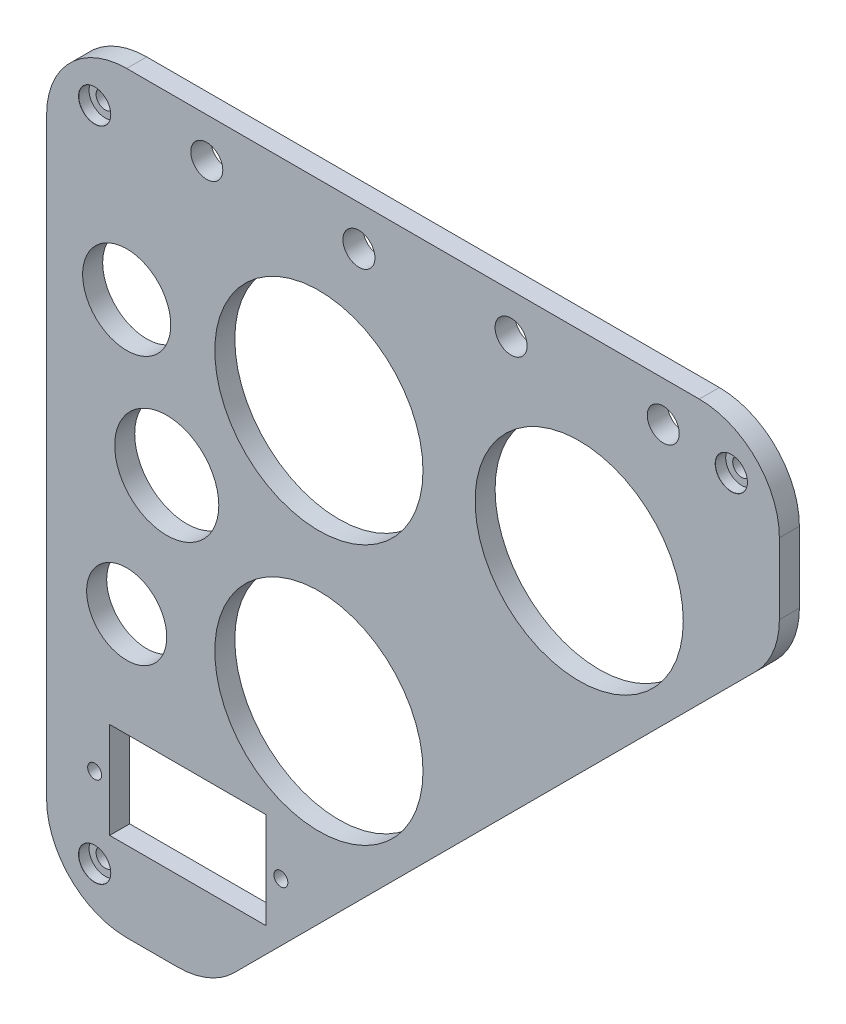
SolidWorks part; units mm, degrees
ref_plane "Piano frontale" through (0, 0, 0) normal (0, 0, 1) x (1, 0, 0)
ref_plane "Piano superiore" through (0, 0, 0) normal (0, 1, 0) x (1, 0, 0)
ref_plane "Piano destro" through (0, 0, 0) normal (1, 0, 0) x (0, 0, -1)
sketch "Schizzo1" plane through (0, 0, 0) normal (0, 0, 1) x (1, 0, 0)
  line L0 (0, 20) -> (0, 168)
  line L1 (20, 188) -> (163, 188)
  line L2 (183, 168) -> (183, 150.2843)
  line L3 (177.1421, 136.1421) -> (46.8579, 5.8579)
  line L4 (32.7157, 0) -> (20, 0)
  arc A0 (0, 168) -> (20, 188) centre (20, 168) cw
  arc A1 (0, 20) -> (20, 0) centre (20, 20) ccw
  arc A2 (46.8579, 5.8579) -> (32.7157, 0) centre (32.7157, 20) cw
  arc A3 (183, 150.2843) -> (177.1421, 136.1421) centre (163, 150.2843) cw
  arc A4 (163, 188) -> (183, 168) centre (163, 168) cw
  point P8 (0, 188)
  point P11 (0, 0)
  point P14 (41, 0)
  point P17 (183, 142)
  point P20 (183, 188)
  dimension "D5" = 20
  dimension "D1" = 183
  dimension "D2" = 46
  dimension "D3" = 45
  dimension "D4" = 41
extrude "Estrusione-Estrusione1" add sketch "Schizzo1" along normal blind 5
hole_wizard "Foro lamato per Vite M4 a testa cilindrica piana-1" positions "Schizzo3" profile "Schizzo4" counterbore size "M4" standard "ISO" end condition through all
sketch "Schizzo3" plane through (0, 0, 5) normal (0, 0, 1) x (1, 0, 0)
  line L2 (163, 188) -> (20, 188) construction
  line L3 (20, 0) -> (32.7157, 0) construction
  line L4 (0, 168) -> (0, 20) construction
  line L5 (183, 150.2843) -> (183, 168) construction
  point P0 (12, 176)
  point P2 (12, 12)
  point P10 (171, 176)
  dimension "D1" = 12
  dimension "D2" = 12
  dimension "D3" = 12
  dimension "D4" = 12
sketch "Schizzo4" plane through (12, 176, 5) normal (1, 0, 0) x (0, -1, 0)
  line L0 (0, 0) -> (0, 5)
  line L1 (0, 5) -> (2.25, 5)
  line L3 (2.25, 5) -> (2.25, 2.6)
  line L4 (4, 2.6) -> (2.25, 2.6)
  line L5 (4, 2.6) -> (4, 0.025)
  line L6 (4, 0.025) -> (4.025, 0)
  line L7 (4.025, 0) -> (0, 0)
  line L8 (-4, 0.025) -> (-4.025, 0) construction
  line L11 (0, -6.35) -> (0, 107.95) construction
  dimension "Thru Hole Dia." = 4.5
  dimension "Thru Hole Depth" = 5
  dimension "C'Bore Dia." = 8
  dimension "C'Bore Depth" = 2.6
  dimension "Near C'Sink Dia." = 8.05
  dimension "Near C'Sink Angle" = 90
sketch "Schizzo5" plane through (0, 0, 5) normal (0, 0, 1) x (1, 0, 0)
  line L0 (15.75, 20) -> (15.75, 44)
  line L1 (54.75, 20) -> (15.75, 20)
  line L2 (54.75, 44) -> (54.75, 20)
  line L3 (15.75, 44) -> (54.75, 44)
  line L4 (163, 188) -> (20, 188) construction
  line L5 (0, 168) -> (0, 20) construction
  circle A1 centre (12, 32) radius 1.75
  circle A2 centre (58.5, 32) radius 1.75
  circle A3 centre (20, 70) radius 10
  circle A4 centre (20, 138) radius 11
  circle A5 centre (30, 105) radius 13
  circle A10 centre (40, 178) radius 4
  circle A12 centre (78, 178) radius 4
  circle A13 centre (116, 178) radius 4
  circle A14 centre (154, 178) radius 4
  circle A15 centre (12, 12) radius 2.25 construction
  circle A16 centre (12, 12) radius 2.25 construction
  circle A17 centre (68, 138) radius 26
  circle A18 centre (133, 138) radius 26
  circle A19 centre (68, 73) radius 26
  point P14 (0, 0)
  point P17 (15.75, 32)
  point P34 (0, 0)
  point P37 (34.5848, 103.5165)
  point P38 (0, 0)
  dimension "pulsante" = 26
  dimension "D4" = 8
  dimension "D7" = 10
  dimension "chiave" = 11
  dimension "interruttore" = 20
  dimension "D16" = 3.5
  dimension "D17" = 52
  dimension "D3" = 38
  dimension "D5" = 10
  dimension "D6" = 40
  dimension "D8" = 33
  dimension "D9" = 20
  dimension "D10" = 3.75
  dimension "D11" = 3.75
  dimension "D12" = 24
  dimension "D13" = 39
  dimension "D14" = 50
  dimension "D15" = 20
  dimension "D18" = 65
  dimension "D19" = 65
  dimension "D20" = 50
  dimension "D21" = 68
  dimension "D22" = 35
  dimension "D2" = 4
extrude "Taglio-Estrusione2" cut sketch "Schizzo5" against normal blind 7
